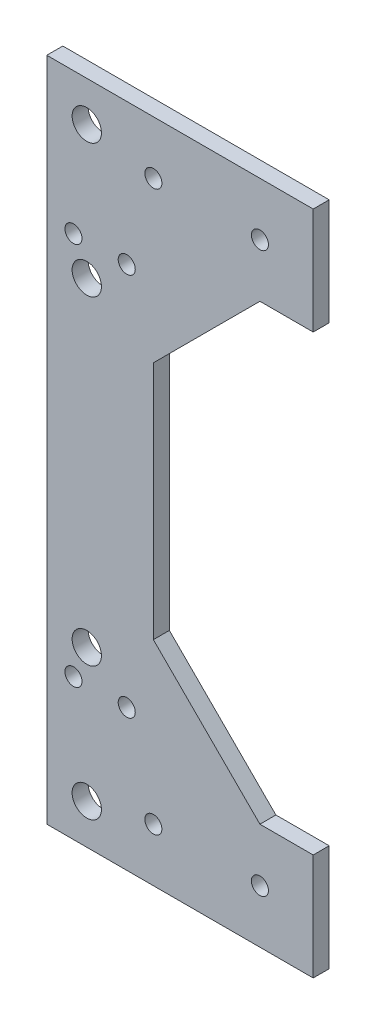
SolidWorks part; units mm, degrees
material "Thornel Mat VMA"
ref_plane "Front Plane" through (0, 0, 0) normal (0, 0, 1) x (1, 0, 0)
ref_plane "Top Plane" through (0, 0, 0) normal (0, 1, 0) x (1, 0, 0)
ref_plane "Right Plane" through (0, 0, 0) normal (1, 0, 0) x (0, 0, -1)
sketch "Sketch1" plane through (0, 0, 0) normal (0, 0, 1) x (1, 0, 0)
  line L0 (-75, -42.5) -> (-75, 42.5) construction
  line L4 (-95, 62.5) -> (-95, -62.5)
  line L5 (-95, -62.5) -> (95, -62.5)
  line L6 (95, -62.5) -> (95, 62.5)
  line L7 (95, 62.5) -> (-95, 62.5)
  line L8 (-95, 62.5) -> (-95, -62.5)
  line L14 (-55, -42.5) -> (-75, -22.5) construction
  line L15 (-75, 22.5) -> (-55, 42.5) construction
  line L16 (-75, -22.5) -> (-75, 22.5)
  line L22 (-55, -42.5) -> (-75, -22.5)
  line L23 (-75, 22.5) -> (-55, 42.5)
  line L26 (-55, 62.5) -> (-95, 62.5)
  line L27 (-55, -62.5) -> (-95, -62.5)
  line L52 (-75, 42.5) -> (75, 42.5) construction
  line L53 (-55, 62.5) -> (-45, 62.5)
  line L55 (-55, 42.5) -> (-45, 42.5)
  line L56 (-45, 62.5) -> (-45, 42.5)
  line L57 (95, -62.5) -> (-95, -62.5) construction
  line L58 (-55, -42.5) -> (-45, -42.5)
  line L60 (-55, -62.5) -> (-45, -62.5)
  line L61 (-45, -42.5) -> (-45, -62.5)
  circle A0 centre (-75, 52.5) radius 1.6 construction
  circle A1 centre (-55, 52.5) radius 1.6 construction
  circle A2 centre (-75, -52.5) radius 1.6 construction
  circle A3 centre (-55, -52.5) radius 1.6 construction
  circle A13 centre (-55, -52.5) radius 1.6
  circle A14 centre (-75, -52.5) radius 1.6
  circle A15 centre (-55, 52.5) radius 1.6
  circle A16 centre (-75, 52.5) radius 1.6
  dimension "D2" = 10
  dimension "D3" = 10
  dimension "D1" = 0
extrude "Extrude1" add sketch "Sketch1" along normal blind 3
sketch "Sketch2" plane through (0, 0, 3) normal (0, 0, 1) x (1, 0, 0)
  circle A0 centre (-80, 36) radius 1.6 construction
  circle A1 centre (-90, 36) radius 1.6 construction
  circle A2 centre (-80, -36) radius 1.6 construction
  circle A3 centre (-90, -36) radius 1.6 construction
  circle A4 centre (-80, 36) radius 1.6
  circle A5 centre (-90, 36) radius 1.6
  circle A6 centre (-80, -36) radius 1.6
  circle A7 centre (-90, -36) radius 1.6
extrude "Cut-Extrude1" cut sketch "Sketch2" against normal blind 26
sketch "Sketch3" plane through (0, 0, 0) normal (0, 0, -1) x (-1, 0, 0)
  circle A0 centre (87.5, 55) radius 2.75 construction
  circle A1 centre (87.5, 30) radius 2.75 construction
  circle A2 centre (87.5, -30) radius 2.75 construction
  circle A3 centre (87.5, -55) radius 2.75 construction
  circle A4 centre (87.5, 55) radius 2.75
  circle A5 centre (87.5, 30) radius 2.75
  circle A6 centre (87.5, -30) radius 2.75
  circle A7 centre (87.5, -55) radius 2.75
extrude "Cut-Extrude2" cut sketch "Sketch3" against normal blind 10
